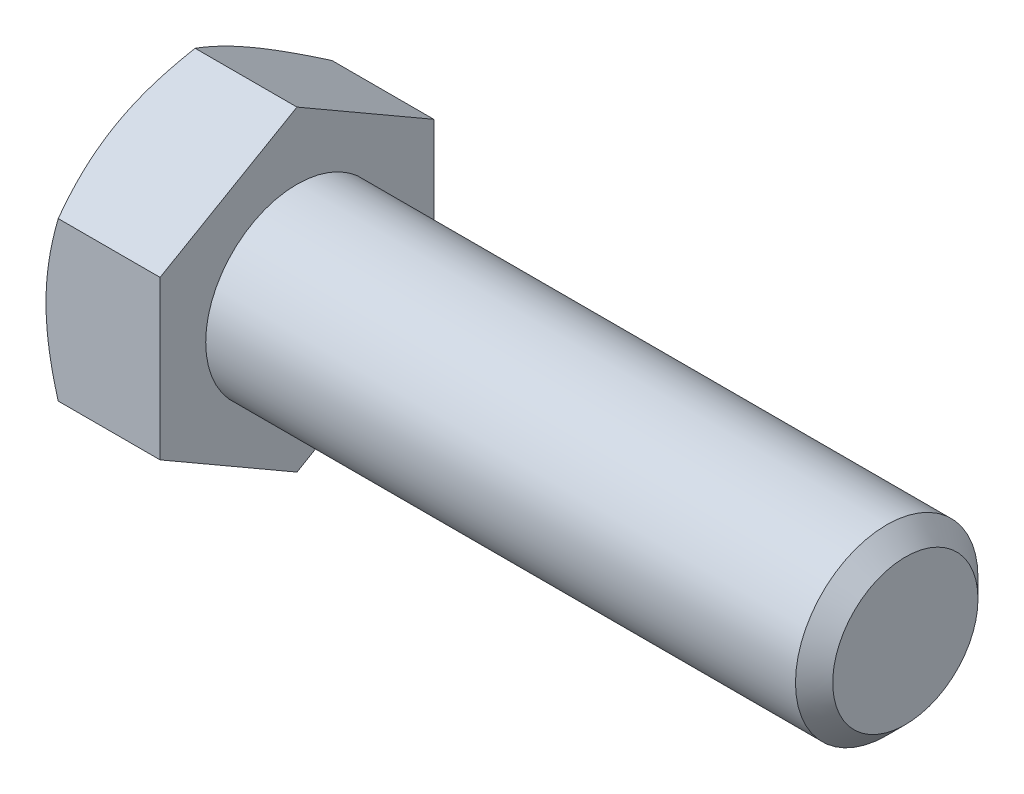
SolidWorks part; units mm, degrees
ref_plane "Front Plane" through (0, 0, 0) normal (0, 0, 1) x (1, 0, 0)
ref_plane "Top Plane" through (0, 0, 0) normal (0, 1, 0) x (1, 0, 0)
ref_plane "Right Plane" through (0, 0, 0) normal (1, 0, 0) x (0, 0, -1)
sketch "Sketch1" plane through (0, 0, 0) normal (0, 0, 1) x (1, 0, 0)
  line L0 (-18.8516, 0) -> (18.8516, 0) construction
  line L1 (18.8516, 4.7625) -> (18.8516, -4.7625) construction
  line L2 (-12.8984, 7.1437) -> (-12.8984, -7.1437) construction
  line L3 (-18.8516, 7.1437) -> (-18.8516, -7.1437) construction
  point P9 (-12.8984, 0)
  point P10 (13.2953, -4.7625)
  dimension "Screw Dia" = 9.525
  dimension "Hex" = 14.2875
  dimension "Head Ht" = 5.9531
  dimension "Screw Lenght" = 31.75
  dimension "D1" = 5.5562
ref_plane "Plane2" through (18.8516, 0, 0) normal (1, 0, 0) x (0, 0, -1)
sketch "Sketch5" plane through (18.8516, 0, 0) normal (1, 0, 0) x (0, 0, -1)
  circle A0 centre (0, 0) radius 4.7625
extrude "Boss-Extrude3" add sketch "Sketch5" against normal up to vertex (31.75 mm away) up to point (-12.8984, 0, 0)
sketch "Sketch9" plane through (18.8516, 0, 0) normal (1, 0, 0) x (0, 0, -1)
  circle A1 centre (0, 0) radius 4.7625
  circle A2 centre (0, 0) radius 4.7625
  dimension "D1" = 0
curve "Helix/Spiral1" pitch 1.5875 height 33.3375 turns 21 parameters "Pitch"=1.5875
chamfer "Chamfer1" distance 0.9715 angle 45 1 edges at (18.8516, 0, -4.7625)
sketch "Sketch10" plane through (0, 0, 0) normal (0, 0, 1) x (1, 0, 0)
  line L0 (18.8516, 4.7625) -> (19.4469, 3.7314)
  line L1 (19.4469, 3.7314) -> (19.6453, 3.7314)
  line L2 (19.6453, 3.7314) -> (20.2406, 4.7625)
  line L3 (18.8516, 4.7625) -> (20.2406, 4.7625)
  line L4 (19.5461, 4.7625) -> (19.5461, 3.7314) construction
  line L5 (19.1492, 4.2469) -> (19.943, 4.2469) construction
  dimension "D1" = 60
  dimension "D2" = 0.1984
  dimension "D3" = 0.7937
sketch "Sketch6" plane through (-12.8984, 0, 0) normal (-1, 0, 0) x (0, 0, 1)
  line L0 (0, 7.1437) -> (0, -7.1437) construction
  line L1 (7.1437, 4.1244) -> (0, 8.2489)
  line L2 (0, 8.2489) -> (-7.1438, 4.1244)
  line L3 (-7.1438, 4.1244) -> (-7.1438, -4.1244)
  line L4 (-7.1438, -4.1244) -> (0, -8.2489)
  line L5 (0, -8.2489) -> (7.1438, -4.1244)
  line L6 (7.1438, -4.1244) -> (7.1437, 4.1244)
  circle A0 centre (0, 0) radius 7.1438 construction
extrude "Boss-Extrude4" add sketch "Sketch6" along normal up to vertex (5.9531 mm away) up to point (-18.8516, -7.1437, 0)
sketch "Sketch7" plane through (-18.8516, 0, 0) normal (-1, 0, 0) x (0, 0, 1)
  circle A0 centre (0, 0) radius 7.1438 construction
  circle A1 centre (0, 0) radius 7.1438
sketch "Sketch8" plane through (-18.8516, 0, 0) normal (-1, 0, 0) x (0, 0, 1)
  circle A0 centre (0, 0) radius 7.1438 construction
  circle A1 centre (0, 0) radius 7.1438
extrude "Cut-Extrude3" cut sketch "Sketch8" against normal through all draft 60 flip side to cut
sketch "Sketch12" plane through (-18.8516, 0, 0) normal (-1, 0, 0) x (0, 0, 1)
  line L0 (0, 5.5007) -> (0, 3.0718) construction
  line L1 (0.2143, 5.5007) -> (0.2143, 3.0718)
  line L2 (-0.2143, 5.5007) -> (-0.2143, 3.0718)
  line L3 (0, 4.7625) -> (0, -4.7625) construction
  arc A0 (0.2143, 5.5007) -> (-0.2143, 5.5007) centre (0, 5.5007) ccw
  arc A1 (-0.2143, 3.0718) -> (0.2143, 3.0718) centre (0, 3.0718) ccw
  circle A3 centre (0, 0) radius 2.8575 construction
  circle A4 centre (0, 0) radius 5.715 construction
  point P2 (0, 4.2862)
  dimension "D1" = 5.715
  dimension "D3" = 11.43
  dimension "D2" = 0.4286
extrude "Cut-Extrude4" cut sketch "Sketch12" against normal blind 0.254
pattern_circular "CirPattern1" count 3 over 360 about axis through (0, 0, 0) along (1, 0, 0) of "Cut-Extrude4"
equation "\"D2@Sketch10\" = \"Pitch@Helix/Spiral1\"*.125"
equation "\"D3@Sketch10\" = \"Pitch@Helix/Spiral1\"*.5"
equation "\"D1@Chamfer1\" = \"Pitch@Helix/Spiral1\"*.612"
equation "\"D1@Sketch12\" = \"Hex@Sketch1\"*.4"
equation "\"D3@Sketch12\" = \"Hex@Sketch1\"*.8"
equation "\"D2@Sketch12\" = \"Hex@Sketch1\"*.03"
equation "\"D1@Sketch1\" = \"Pitch@Helix/Spiral1\"*3.5"
equation "\"D3@Helix/Spiral1\" = \"Screw Lenght@Sketch1\"+\"Pitch@Helix/Spiral1\""
